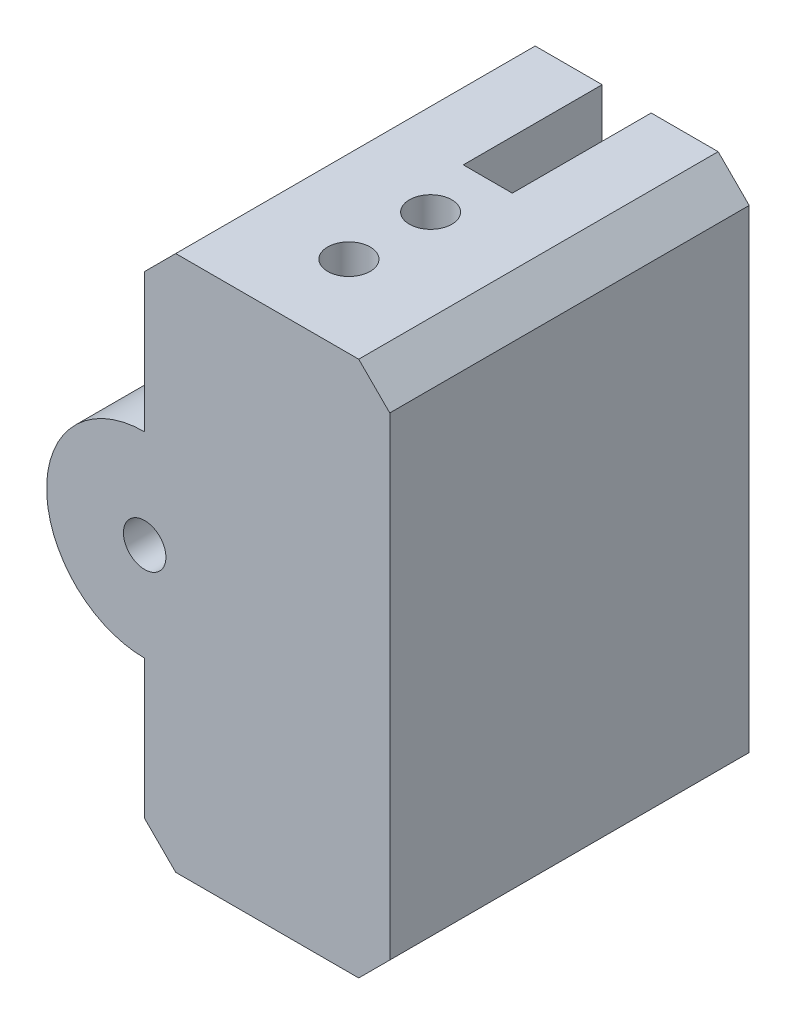
SolidWorks part; units mm, degrees
ref_plane "Front Plane" through (0, 0, 0) normal (0, 0, 1) x (1, 0, 0)
ref_plane "Top Plane" through (0, 0, 0) normal (0, 1, 0) x (1, 0, 0)
ref_plane "Right Plane" through (0, 0, 0) normal (1, 0, 0) x (0, 0, -1)
sketch "Sketch1" plane through (0, 0, 0) normal (0, 1, 0) x (1, 0, 0)
  line L0 (0, 0) -> (0, -17) construction
  line L1 (-7.5, 0) -> (7.5, 0)
  line L2 (-7.5, 0) -> (-7.5, -22)
  line L3 (-7.5, -22) -> (7.5, -22)
  line L4 (7.5, 0) -> (7.5, -22)
  line L5 (-1.5, -8.5) -> (1.5, -8.5)
  line L6 (-1.5, -8.5) -> (-1.5, 0)
  line L7 (-1.5, 0) -> (1.5, 0)
  line L8 (1.5, -8.5) -> (1.5, 0)
  circle A0 centre (0, -12) radius 1.3
  circle A1 centre (0, -17) radius 1.3
  point P5 (0, 0)
  point P12 (0, 0)
  dimension "D6" = 2.6
  dimension "D7" = 5
  dimension "D1" = 8.5
  dimension "D2" = 3
  dimension "D3" = 22
  dimension "D4" = 6
  dimension "D5" = 10
extrude "Boss-Extrude1" add sketch "Sketch1" along normal blind 32.8
chamfer "Chamfer1" distance 1.9 angle 45 2 edges at (7.5, 32.8, 11) (7.5, 0, 11)
chamfer "Chamfer2" distance 1.9 angle 45 2 edges at (-7.5, 0, 11) (-7.5, 32.8, 11)
sketch "Sketch2" plane through (0, 0, 0) normal (0, 0, -1) x (-1, 0, 0)
  line L0 (7.5, 30.9) -> (7.5, 1.9) construction
  line L1 (1.5, 32.8) -> (1.5, 0) construction
  circle A0 centre (7.5, 16.4) radius 6
extrude "Boss-Extrude2" add sketch "Sketch2" against normal blind 22
sketch "Sketch3" plane through (0, 0, 0) normal (0, 0, -1) x (-1, 0, 0)
  circle A0 centre (7.5, 16.4) radius 1.3
  dimension "D1" = 2.6
extrude "Cut-Extrude1" cut sketch "Sketch3" against normal through all both and the other way through all
